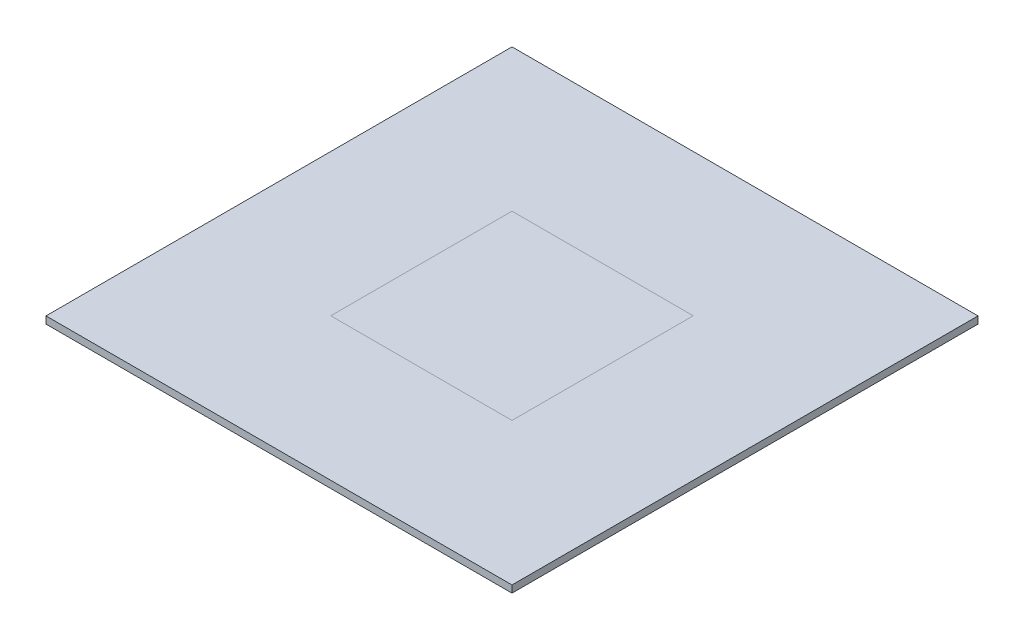
SolidWorks part; units mm, degrees
ref_plane "Front Plane" through (0, 0, 0) normal (0, 0, 1) x (1, 0, 0)
ref_plane "Top Plane" through (0, 0, 0) normal (0, 1, 0) x (1, 0, 0)
ref_plane "Right Plane" through (0, 0, 0) normal (1, 0, 0) x (0, 0, -1)
sketch "Sketch1" plane through (0, 0, 0) normal (0, 1, 0) x (1, 0, 0)
  line L1 (-45, 45) -> (45, 45)
  line L2 (-45, 45) -> (-45, -45)
  line L3 (-45, -45) -> (45, -45)
  line L4 (45, 45) -> (45, -45)
  line L5 (-45, 45) -> (45, -45) construction
  line L6 (-45, -45) -> (45, 45) construction
  point P0 (0, 0)
  dimension "D1" = 90
extrude "Boss-Extrude1" add sketch "Sketch1" along normal blind 1.375
sketch "Sketch2" plane through (0, 1.375, 0) normal (0, 1, 0) x (1, 0, 0)
  line L1 (-17.5, 17.5) -> (17.5, 17.5)
  line L2 (-17.5, 17.5) -> (-17.5, -17.5)
  line L3 (-17.5, -17.5) -> (17.5, -17.5)
  line L4 (17.5, 17.5) -> (17.5, -17.5)
  line L5 (-17.5, 17.5) -> (17.5, -17.5) construction
  line L6 (-17.5, -17.5) -> (17.5, 17.5) construction
  point P0 (0, 0)
  dimension "D1" = 35
surface "Surface-Plane1" sketch "Sketch2"
move or copy body "Body-Move/Copy1" bodies to move or copy 102 copy no translate (0, 0.018, 0)
